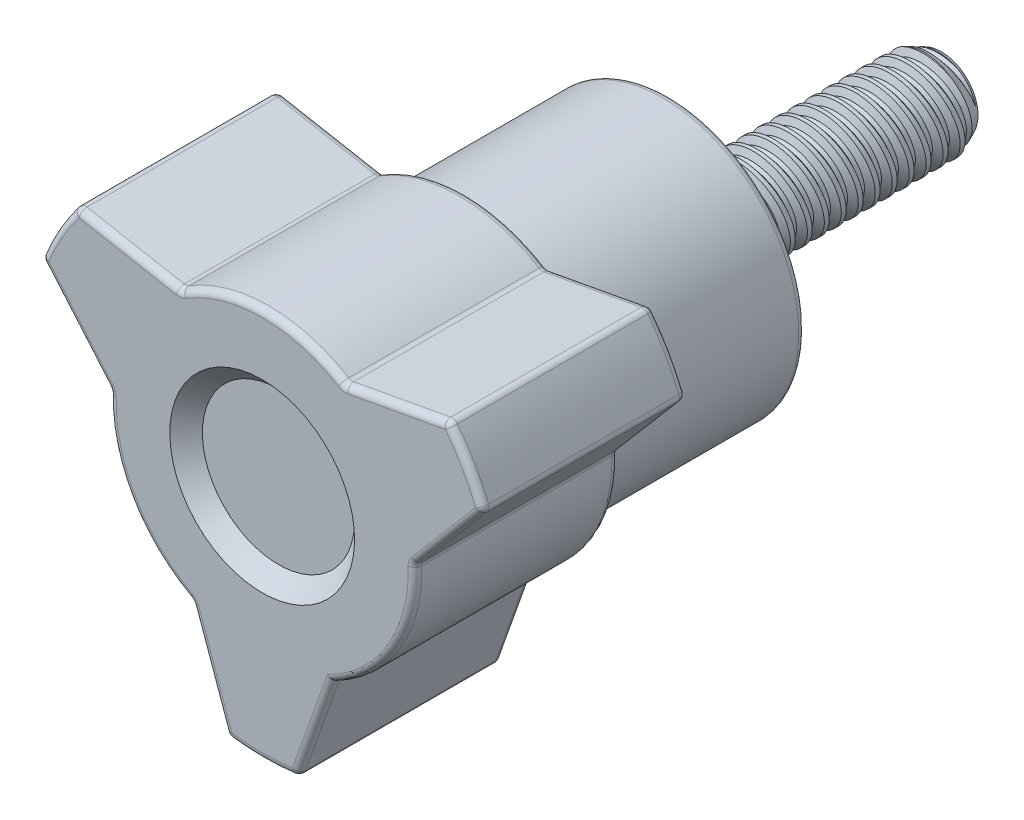
SolidWorks part; units mm, degrees
ref_plane "Front" through (0, 0, 0) normal (0, 0, 1) x (1, 0, 0)
ref_plane "Top" through (0, 0, 0) normal (0, 1, 0) x (1, 0, 0)
ref_plane "Right" through (0, 0, 0) normal (1, 0, 0) x (0, 0, -1)
sketch "Sketch1" plane through (0, 0, 0) normal (1, 0, 0) x (0, 0, -1)
  line L0 (6.35, 0) -> (-6.35, 0)
  line L1 (-6.35, 2.0828) -> (-6.35, 4.5339) construction
  line L4 (-6.35, 2.0828) -> (6.35, 2.0828)
  line L5 (6.35, 2.0828) -> (6.35, 0)
  line L6 (-6.35, 0) -> (-6.35, 2.0828)
  line L7 (-8.5598, 0) -> (-6.35, 0) construction
  line L10 (-6.35, -2.0828) -> (6.35, -2.0828) construction
  dimension "Screw Dia" = 4.1656
  dimension "Thread Length" = 12.7
revolve "Revolve1" add sketch "Sketch1" angle 360 about L7
sketch "Sketch2" plane through (0, 0, 0) normal (1, 0, 0) x (0, 0, -1)
  line L0 (-6.35, 2.0828) -> (-6.35, -2.0828) construction
  line L1 (-6.35, -2.0828) -> (-5.5562, -2.0828) construction
  line L2 (-5.5562, -2.0828) -> (-6.35, 2.0828) construction
  line L3 (-6.35, 2.0828) -> (-6.2525, 2.1014) construction
  line L4 (-6.2525, 2.1014) -> (-5.5703, 2.2314)
  line L5 (-5.5703, 2.2314) -> (-5.7335, 1.7629)
  line L6 (-5.7335, 1.7629) -> (-5.9285, 1.7258)
  line L7 (-5.9285, 1.7258) -> (-6.2525, 2.1014)
  line L8 (-5.831, 1.7443) -> (-5.9114, 2.1664) construction
  line L9 (-6.35, 2.0828) -> (-5.8955, 2.0828) construction
  line L10 (-5.8955, 2.0828) -> (-5.1017, -2.0828) construction
  line L11 (-5.1017, -2.0828) -> (-5.5562, -2.0828) construction
  line L12 (-6.35, -2.0828) -> (6.35, -2.0828) construction
  line L13 (-6.35, 2.0828) -> (6.35, 2.0828) construction
  line L14 (-6.35, 0) -> (-6.35, 2.0828) construction
  line L15 (-6.35, -0.1622) -> (-4.6472, 0.1622) construction
  point P19 (-5.4986, 0)
  dimension "D1" = 0.0992
  dimension "D2" = 0.1984
  dimension "D3" = 60
  dimension "Thread Pitch" = 0.7937
  dimension "D4" = 0.7937
revolve "Cut-Revolve1" cut sketch "Sketch2" angle 360 about L15
pattern_linear "LPattern1" count 16 spacing 0.7937 along (0, 0, -1) count 2 spacing 0.7937 along (0, 0, 1) of "Cut-Revolve1"
sketch "Sketch5" plane through (0, 0, 0) normal (1, 0, 0) x (0, 0, -1)
  line L0 (-6.35, 0) -> (6.35, 0) construction
  line L2 (-6.35, 6.35) -> (-15.875, 6.35)
  line L3 (-15.875, 6.35) -> (-15.875, 11.1125)
  line L4 (-6.35, 0) -> (-6.35, -6.35) construction
  line L5 (-6.35, 0) -> (-6.35, 2.0828) construction
  line L7 (-25.4, 0) -> (-6.35, 0) construction
  line L8 (-6.35, 2.0828) -> (-6.35, -2.0828) construction
  line L10 (-6.35, 6.35) -> (-6.35, 0)
  line L12 (-25.4, 11.1125) -> (-15.875, 11.1125)
  line L13 (-25.4, 11.1125) -> (-25.4, 0)
  line L14 (-15.875, -6.35) -> (-15.875, -11.1125) construction
  line L18 (-6.35, 0) -> (-25.4, 0)
  dimension "D1" = 11.1125
  dimension "D" = 9.525
  dimension "B" = 12.7
  dimension "C" = 9.525
  dimension "A" = 22.225
revolve "Revolve3" add sketch "Sketch5" angle 360 about L0
sketch "Sketch6" plane through (0, 0, 25.4) normal (0, 0, 1) x (1, 0, 0)
  line L0 (0, 0) -> (0, 14.2875) construction
  line L1 (0, 0) -> (12.3733, -7.1438) construction
  line L2 (0, 0) -> (9.6237, 5.5562) construction
  line L3 (8.6914, 6.9244) -> (3.8351, 6.027)
  line L4 (0, 14.2875) -> (0, 7.1437)
  line L5 (6.1867, -3.5719) -> (12.3733, -7.1438)
  line L6 (10.3424, 4.0648) -> (7.1371, 0.3078)
  arc A0 (3.8351, 6.027) -> (0, 7.1437) centre (0, 0) ccw
  arc A2 (10.3424, 4.0648) -> (8.6914, 6.9244) centre (0, 0) ccw
  arc A3 (7.1371, 0.3078) -> (6.1867, -3.5719) centre (0, 0) cw
  arc A4 (12.3733, -7.1438) -> (0, 14.2875) centre (0, 0) ccw
  circle A5 centre (0, 0) radius 7.1438 construction
  circle A6 centre (0, 0) radius 11.1125 construction
  dimension "D2" = 14.2875
  dimension "D3" = 60
  dimension "D4" = 3.302
  dimension "D5" = 6.604
  dimension "D6" = 14.2875
  dimension "D1" = 120
extrude "Cut-Extrude1" cut sketch "Sketch6" against normal up to next
pattern_circular "CirPattern1" count 3 over 360 about axis through (0, 0, 0) along (0, 0, 1) of "Cut-Extrude1"
sketch "Sketch10" plane through (0, 0, 0) normal (1, 0, 0) x (0, 0, -1)
  line L0 (-25.4, 4.318) -> (-25.4, -4.318) construction
  line L1 (-25.4, 11.1125) -> (-25.4, 0) construction
  line L2 (-25.4, 7.1438) -> (-25.4, -7.1437) construction
  line L3 (-6.35, 0) -> (-25.4, 0) construction
  line L4 (-25.4, 0) -> (-25.4, 4.318)
  line L5 (-25.4, 4.318) -> (-24.638, 3.556)
  line L6 (-24.638, 3.556) -> (-24.638, 0)
  line L7 (-24.638, 0) -> (-25.4, 0)
  line L8 (6.35, 0) -> (-25.4, 0) construction
  point P6 (-25.4, 0)
  dimension "D1" = 45
  dimension "D2" = 8.636
  dimension "D3" = 0.762
revolve "Cut-Revolve3" cut sketch "Sketch10" angle 360 about L8
fillet "Fillet4" radius 0.3175 36 edges at (0, -6.35, 6.35) (6.1867, -3.5719, 15.875) (6.1867, -3.5719, 25.4) (6.2633, 6.4757, 15.875) (-8.6914, 6.9244, 20.6375) (-9.6237, 5.5562, 25.4) (-10.3424, 4.0648, 20.6375) (-9.6237, 5.5562, 15.875) (-1.651, -10.9892, 20.6375) (0, -11.1125, 15.875) (-2.4765, -8.662, 15.875) (-3.302, -6.3348, 20.6375) (-7.1371, 0.3078, 20.6375) (-6.1867, -3.5719, 15.875) (-8.7398, 2.1863, 15.875) (-8.7398, 2.1863, 25.4) (-6.1867, -3.5719, 25.4) (-2.4765, -8.662, 25.4) (0, -11.1125, 25.4) (2.4765, -8.662, 25.4) (1.651, -10.9892, 20.6375) (2.4765, -8.662, 15.875) (8.7398, 2.1863, 15.875) (7.1371, 0.3078, 20.6375) (8.7398, 2.1863, 25.4) (10.3424, 4.0648, 20.6375) (9.6237, 5.5562, 15.875) (9.6237, 5.5562, 25.4) (8.6914, 6.9244, 20.6375) (6.2633, 6.4757, 25.4) (3.8351, 6.027, 20.6375) (-3.8351, 6.027, 20.6375) (0, 7.1438, 25.4) (-6.2633, 6.4757, 25.4) (-6.2633, 6.4757, 15.875) (0, 7.1438, 15.875)
sketch "Sketch11" plane through (0, 0, 0) normal (1, 0, 0) x (0, 0, -1)
  line L0 (5.5562, 2.0828) -> (6.35, 1.7127)
  line L1 (-6.35, 2.0828) -> (6.35, 2.0828) construction
  line L2 (6.35, 2.0828) -> (6.35, 0) construction
  line L3 (6.35, 1.7127) -> (6.35, 2.0828)
  line L4 (6.35, 2.0828) -> (5.5562, 2.0828)
  line L5 (0, 0) -> (6.35, 0) construction
  dimension "D1" = 25
  dimension "D2" = 0.7937
revolve "Cut-Revolve4" cut sketch "Sketch11" angle 360 about L5
sketch "Sketch12" plane through (0, 0, 6.35) normal (0, 0, -1) x (-1, 0, 0)
  circle A0 centre (0, 0) radius 6.35 construction
  circle A1 centre (0, 0) radius 6.35
equation "\"D1@Sketch2\"=\"Thread Pitch@Sketch2\"/8"
equation "\"D2@Sketch2\"=\"Thread Pitch@Sketch2\"/4"
equation "\"D4@Sketch2\"=\"Thread Pitch@Sketch2\""
equation "\"D3@LPattern1\"=\"Thread Pitch@Sketch2\""
equation "\"D4@LPattern1\"=\"Thread Pitch@Sketch2\""
equation "\"D1@LPattern1\"=\"Thread Length@Sketch1\"/\"Thread Pitch@Sketch2\""
equation "\"D2@Sketch6\" = \"B@Sketch5\"*1.125"
equation "\"D1@Sketch5\" = \"A@Sketch5\"/2"
equation "\"D2@Sketch11\" = \"Thread Pitch@Sketch2\""
equation "\"D6@Sketch6\" = \"D1@Sketch5\"+.125"
